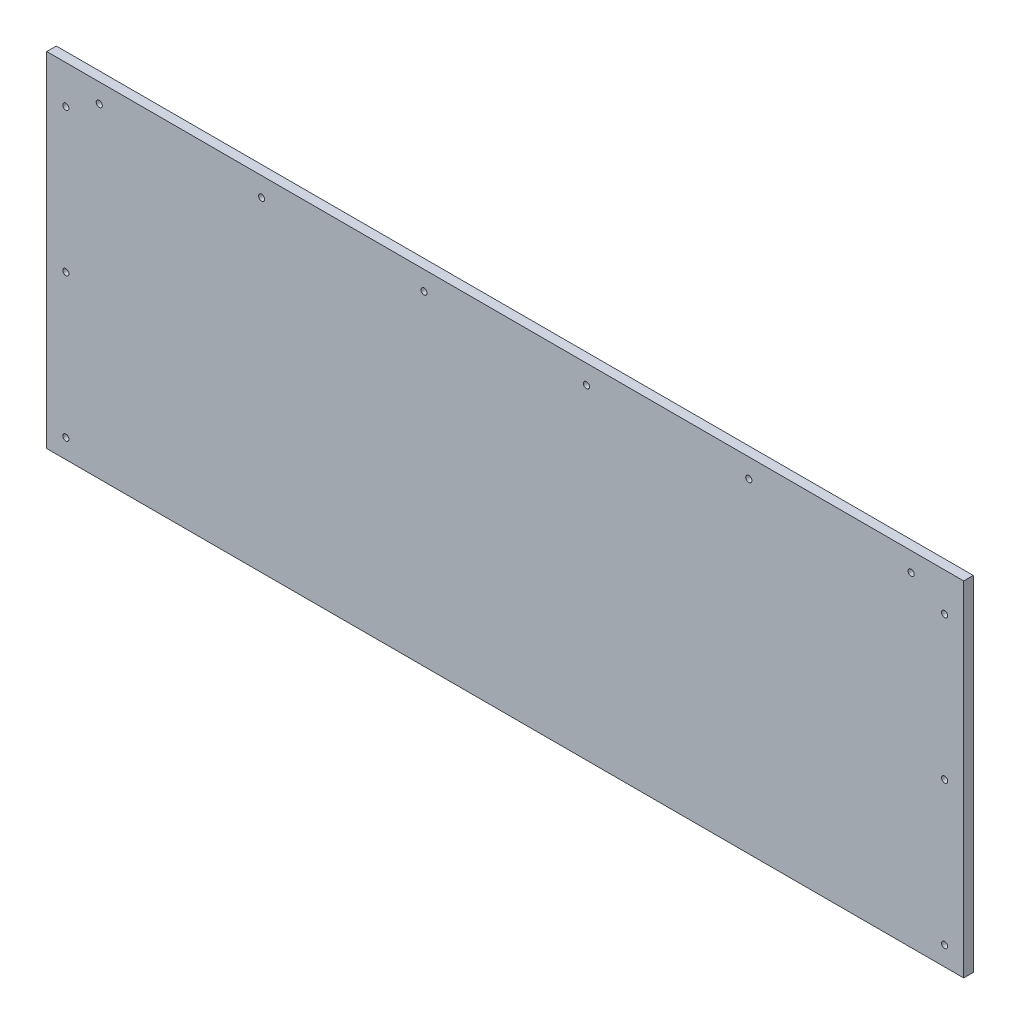
SolidWorks part; units mm, degrees
ref_plane "Front Plane" through (0, 0, 0) normal (0, 0, 1) x (1, 0, 0)
ref_plane "Top Plane" through (0, 0, 0) normal (0, 1, 0) x (1, 0, 0)
ref_plane "Right Plane" through (0, 0, 0) normal (1, 0, 0) x (0, 0, -1)
sketch "Sketch1" plane through (0, 0, 0) normal (0, 0, 1) x (1, 0, 0)
  line L1 (0, 0) -> (609.6, 0)
  line L2 (0, 0) -> (0, 228.6)
  line L3 (0, 228.6) -> (609.6, 228.6)
  line L4 (609.6, 0) -> (609.6, 228.6)
  dimension "D1" = 228.6
  dimension "D2" = 609.6
extrude "Boss-Extrude1" add sketch "Sketch1" along normal blind 6.35 contours L2 L3 L4 L1
sketch "Sketch2" plane through (0, 0, 6.35) normal (0, 0, 1) x (1, 0, 0)
  line L0 (0, 0) -> (0, 228.6) construction
  line L1 (0, 228.6) -> (609.6, 228.6) construction
  line L2 (304.8, 228.6) -> (304.8, 0) construction
  line L3 (0, 0) -> (609.6, 0) construction
  circle A0 centre (12.7, 203.2) radius 2.032
  circle A3 centre (12.7, 107.95) radius 2.032
  circle A4 centre (12.7, 12.7) radius 2.032
  circle A5 centre (596.9, 12.7) radius 2.032
  circle A6 centre (596.9, 107.95) radius 2.032
  circle A7 centre (596.9, 203.2) radius 2.032
  dimension "D3" = 4.064
  dimension "D4" = 3
  dimension "D1" = 12.7
  dimension "D2" = 25.4
extrude "Cut-Extrude4" cut sketch "Sketch2" against normal through all contours A0 | A3 | A4 | A5 | A6 | A7
sketch "Sketch4" plane through (0, 0, 6.35) normal (0, 0, 1) x (1, 0, 0)
  line L0 (0, 228.6) -> (609.6, 228.6) construction
  line L1 (0, 0) -> (0, 228.6) construction
  circle A0 centre (34.925, 215.9) radius 2.032
  circle A1 centre (142.875, 215.9) radius 2.032
  circle A2 centre (250.825, 215.9) radius 2.032
  circle A3 centre (358.775, 215.9) radius 2.032
  circle A4 centre (466.725, 215.9) radius 2.032
  circle A5 centre (574.675, 215.9) radius 2.032
  dimension "D1" = 4.064
  dimension "D2" = 12.7
  dimension "D3" = 34.925
  dimension "D4" = 107.95
extrude "Cut-Extrude7" cut sketch "Sketch4" against normal through all
